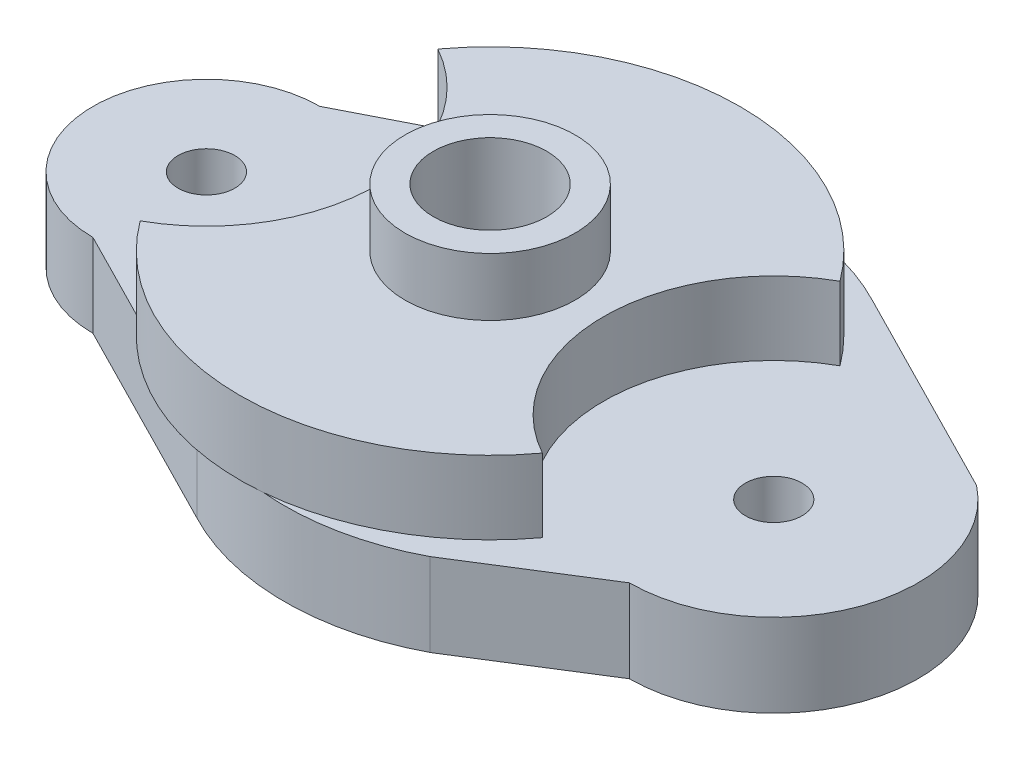
SolidWorks part; units mm, degrees
ref_plane "Front Plane" through (0, 0, 0) normal (0, 0, 1) x (1, 0, 0)
ref_plane "Top Plane" through (0, 0, 0) normal (0, 1, 0) x (1, 0, 0)
ref_plane "Right Plane" through (0, 0, 0) normal (1, 0, 0) x (0, 0, -1)
sketch "Sketch2" plane through (0, 0, 0) normal (0, 1, 0) x (1, 0, 0)
  circle A0 centre (0, 0) radius 6.35
  circle A1 centre (0, 0) radius 9.525
  dimension "D1" = 12.7
  dimension "D2" = 19.05
extrude "Boss-Extrude1" add sketch "Sketch2" along normal blind 14.7
sketch "Sketch3" plane through (0, 0, 0) normal (0, -1, 0) x (1, 0, 0)
  line L0 (28.575, 0) -> (31.75, 0)
  line L2 (-31.75, -12.7) -> (-8.0582, -24.7686)
  line L3 (41.75, -12.7) -> (18.0582, -24.7686)
  line L4 (31.75, 16.1645) -> (18.0582, 24.7686)
  line L5 (-31.75, 12.7) -> (-8.0582, 24.7686)
  arc A0 (18.0582, 24.7686) -> (-8.0582, 24.7686) centre (5, 0) ccw
  circle A1 centre (-31.75, 0) radius 3.175
  circle A2 centre (31.75, 0) radius 3.175
  arc A3 (-31.75, 12.7) -> (-31.75, -12.7) centre (-31.75, 0) ccw
  arc A4 (41.75, -12.7) -> (31.75, 16.1645) centre (31.75, 0) ccw
  arc A5 (-8.0582, -24.7686) -> (18.0582, -24.7686) centre (5, 0) ccw
  circle A6 centre (0, 0) radius 6.35 construction
  dimension "D1" = 63.5
  dimension "D2" = 31.75
extrude "Boss-Extrude2" add sketch "Sketch3" along normal blind 9.3 contours L2 A5 L3 A4 L4 A0 L5 A3
sketch "Sketch4" plane through (0, 0, 0) normal (0, 1, 0) x (1, 0, 0)
  circle A0 centre (0, 0) radius 6.35
extrude "Cut-Extrude1" cut sketch "Sketch4" against normal blind 2540
sketch "Sketch5" plane through (0, 0, 0) normal (0, 1, 0) x (1, 0, 0)
  circle A0 centre (-31.75, 0) radius 3.175
  circle A1 centre (31.75, 0) radius 3.175
  circle A2 centre (0, 0) radius 9.525 construction
  circle A3 centre (0, 0) radius 6.35 construction
  dimension "D1" = 6.35
  dimension "D2" = 6.35
  dimension "D3" = 31.75
  dimension "D4" = 31.75
extrude "Cut-Extrude2" cut sketch "Sketch5" against normal blind 2540
sketch "Sketch6" plane through (0, 0, 0) normal (0, 1, 0) x (1, 0, 0)
  circle A0 centre (0, 0) radius 7.3204
  circle A1 centre (0, 0) radius 28
extrude "Boss-Extrude3" add sketch "Sketch6" along normal blind 8.2
sketch "Sketch8" plane through (0, 8.2, 0) normal (0, 1, 0) x (1, 0, 0)
  circle A0 centre (-31.75, 0) radius 19.05
  circle A1 centre (31.75, 0) radius 19.05
  dimension "D1" = 38.1
  dimension "D2" = 38.1
extrude "Cut-Extrude3" cut sketch "Sketch8" against normal blind 8.2
